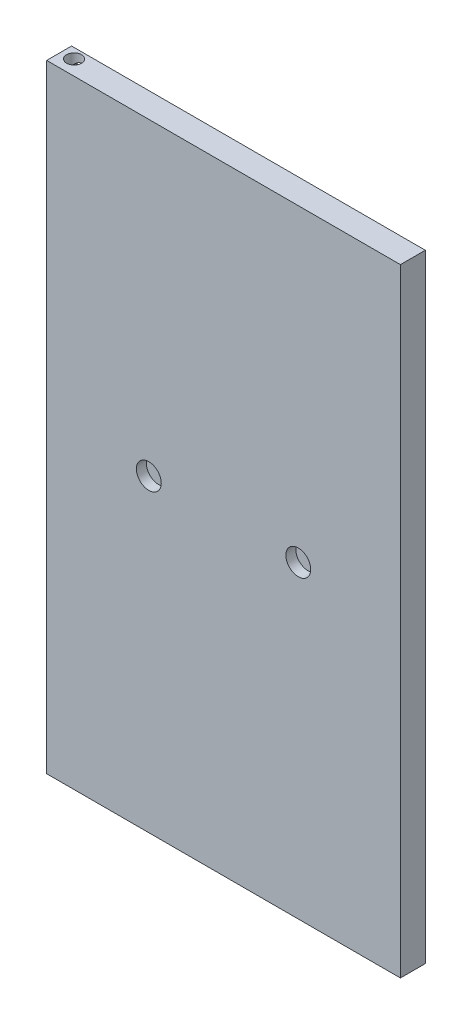
SolidWorks part; units mm, degrees
material "Oak"
ref_plane "Front Plane" through (0, 0, 0) normal (0, 0, 1) x (1, 0, 0)
ref_plane "Top Plane" through (0, 0, 0) normal (0, 1, 0) x (1, 0, 0)
ref_plane "Right Plane" through (0, 0, 0) normal (1, 0, 0) x (0, 0, -1)
sketch "Sketch1" plane through (0, 0, 0) normal (0, 0, 1) x (1, 0, 0)
  line L1 (-90.17, 157.48) -> (90.17, 157.48)
  line L2 (-90.17, 157.48) -> (-90.17, -157.48)
  line L3 (-90.17, -157.48) -> (90.17, -157.48)
  line L4 (90.17, 157.48) -> (90.17, -157.48)
  line L5 (-90.17, 157.48) -> (90.17, -157.48) construction
  line L6 (-90.17, -157.48) -> (90.17, 157.48) construction
  point P0 (0, 0)
  dimension "D1" = 180.34
  dimension "D2" = 314.96
extrude "Boss-Extrude1" add sketch "Sketch1" against normal blind 12.7
ref_plane "Plane1" through (0, 0, -12.7) normal (0, 0, -1) x (-1, 0, 0)
sketch "Sketch2" plane through (0, 0, -12.7) normal (0, 0, -1) x (-1, 0, 0)
  line L0 (-90.17, -157.48) -> (-90.17, 157.48) construction
  line L2 (-90.17, 157.48) -> (90.17, 157.48) construction
  line L7 (-74.93, -142.24) -> (74.93, -142.24)
  line L8 (-74.93, -142.24) -> (-74.93, 144.78)
  line L9 (-74.93, 144.78) -> (74.93, 144.78)
  line L10 (74.93, -142.24) -> (74.93, 144.78)
  dimension "D1" = 287.02
  dimension "D2" = 149.86
  dimension "D3" = 15.24
  dimension "D4" = 12.7
ref_plane "Plane3" through (0, 0, 0) normal (0, 0, 1) x (1, 0, 0)
sketch "Sketch4" plane through (0, 0, 0) normal (0, 0, 1) x (1, 0, 0)
  line L0 (-90.17, -157.48) -> (90.17, -157.48) construction
  line L2 (-90.17, 157.48) -> (-90.17, -157.48) construction
  circle A0 centre (-38.1, 0) radius 6.35
  circle A1 centre (38.1, 0) radius 6.35
  point P4 (0, 0)
  dimension "D1" = 76.2
  dimension "D2" = 12.7
  dimension "D3" = 12.7
  dimension "D4" = 157.48
  dimension "D5" = 52.07
  dimension "D6" = 38.1
extrude "Cut-Extrude2" cut sketch "Sketch4" against normal blind 5.08
ref_plane "Plane4" through (0, 0, -112.7) normal (0, 0, -1) x (-1, 0, 0)
ref_plane "Plane6" through (0, 0, -12.7) normal (0, 0, -1) x (-1, 0, 0)
sketch "Sketch6" plane through (0, 0, -12.7) normal (0, 0, -1) x (-1, 0, 0)
  line L0 (-90.17, 157.48) -> (90.17, 157.48) construction
  line L2 (90.17, 157.48) -> (90.17, -157.48) construction
  line L5 (90.17, -157.48) -> (-90.17, -157.48) construction
  circle A0 centre (83.7599, 149.86) radius 3.81
  circle A1 centre (83.82, -149.86) radius 3.81
  point P8 (0, 0)
  point P13 (0, 0)
  point P15 (84.5338, -151.8271)
  dimension "D1" = 7.62
  dimension "D7" = 7.62
  dimension "D2" = 7.62
  dimension "D3" = 7.62
  dimension "D4" = 6.4101
  dimension "D5" = 299.72
  dimension "D6" = 6.35
extrude "Cut-Extrude3" cut sketch "Sketch6" against normal blind 5.08
ref_plane "Plane7" through (0, 157.48, 0) normal (0, 1, 0) x (1, 0, 0)
sketch "Sketch7" plane through (0, 157.48, 0) normal (0, 1, 0) x (1, 0, 0)
  line L4 (90.17, 0) -> (-90.17, 0) construction
  line L5 (-90.17, 12.7) -> (-90.17, 0) construction
  circle A1 centre (-83.82, 7.62) radius 3.81
  dimension "D1" = 7.62
  dimension "D2" = 7.62
  dimension "D3" = 6.35
extrude "Cut-Extrude4" cut sketch "Sketch7" against normal blind 7.62
ref_plane "Plane8" through (0, -157.48, 0) normal (0, -1, 0) x (-1, 0, 0)
sketch "Sketch8" plane through (0, -157.48, 0) normal (0, -1, 0) x (-1, 0, 0)
  line L3 (90.17, 12.7) -> (90.17, 0) construction
  line L5 (90.17, 0) -> (-90.17, 0) construction
  circle A1 centre (83.82, 7.62) radius 3.81
  point P6 (35.8688, 48.8677)
  point P10 (32.5337, 53.3779)
  point P11 (84.6993, 0)
  dimension "D1" = 7.62
  dimension "D2" = 6.35
  dimension "D3" = 7.62
extrude "Cut-Extrude5" cut sketch "Sketch8" against normal blind 7.62
